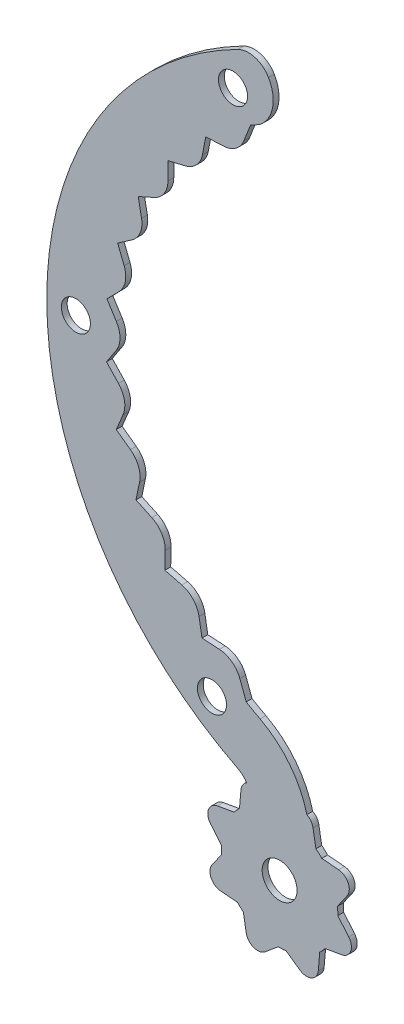
SolidWorks part; units mm, degrees
material "3003 Alaşım"
ref_plane "Ön Düzlem" through (0, 0, 0) normal (0, 0, 1) x (1, 0, 0)
ref_plane "Üst Düzlem" through (0, 0, 0) normal (0, 1, 0) x (1, 0, 0)
ref_plane "Sağ Düzlem" through (0, 0, 0) normal (1, 0, 0) x (0, 0, -1)
sketch "Çizim1" plane through (0, 0, 0) normal (0, 0, 1) x (1, 0, 0)
  line L0 (-50, 0) -> (-25, 0) construction
  line L1 (-25, 74.7114) -> (-25, -57.8833) construction
  line L3 (-25, 43.3013) -> (-26.1465, 40.3921)
  line L10 (-32.6937, 37.73) -> (-33.2521, 34.7773)
  line L11 (-32.6937, 37.73) -> (-29.6915, 37.8626)
  line L12 (-39.1845, 30.9355) -> (-36.2603, 31.6283)
  line L13 (-39.1845, 30.9355) -> (-39.1797, 27.9304)
  line L14 (-44.2872, 23.0451) -> (-41.5446, 24.2736)
  line L15 (-44.2872, 23.0451) -> (-43.7194, 20.0942)
  line L16 (-47.8209, 14.3384) -> (-45.3571, 16.059)
  line L17 (-47.8209, 14.3384) -> (-46.7103, 11.546)
  line L18 (-49.6606, 5.1236) -> (-47.5629, 7.2754)
  line L19 (-49.6606, 5.1236) -> (-48.0464, 2.5889)
  line L20 (-49.7411, -4.2726) -> (-48.0837, -1.7658)
  line L21 (-49.7411, -4.2726) -> (-47.6805, -6.46)
  line L22 (-48.0594, -13.5175) -> (-46.9011, -10.7445)
  line L23 (-48.0594, -13.5175) -> (-45.6255, -15.28)
  line L24 (-44.6753, -22.2835) -> (-44.057, -19.3426)
  line L25 (-44.6753, -22.2835) -> (-41.9541, -23.5587)
  line L26 (-39.7084, -30.2601) -> (-39.6522, -27.2555)
  line L27 (-39.7084, -30.2601) -> (-36.7965, -31.0028)
  line L28 (-33.3349, -37.1647) -> (-33.8427, -34.2028)
  line L29 (-33.3349, -37.1647) -> (-30.3354, -37.3487)
  line L30 (-25.7378, -42.8669) -> (-26.8343, -39.9385)
  line L31 (-25, -57.0526) -> (-25, -57.8833)
  line L33 (-15, -47.697) -> (-15, -66.5436) construction
  line L34 (-25, -66.5436) -> (-15, -66.5436) construction
  line L35 (-25, -54.5436) -> (-25, -66.5436) construction
  arc A0 (-27.1796, 53.4909) -> (-27.1875, -53.4868) centre (0, 0) ccw
  arc A3 (-23.4461, 44.162) -> (-21.9062, 51.9296) centre (-27.0983, 48.9224) ccw
  arc A4 (-26.1465, 40.3921) -> (-29.6915, 37.8626) centre (-29.8679, 41.8587) cw
  arc A5 (-33.2521, 34.7773) -> (-36.2603, 31.6283) centre (-37.1824, 35.5206) cw
  arc A6 (-39.1797, 27.9304) -> (-41.5446, 24.2736) centre (-43.1797, 27.9241) cw
  arc A7 (-43.7194, 20.0942) -> (-45.3571, 16.059) centre (-47.6474, 19.3384) cw
  arc A8 (-46.7103, 11.546) -> (-47.5629, 7.2754) centre (-50.4271, 10.0677) cw
  arc A9 (-48.0464, 2.5889) -> (-48.0837, -1.7658) centre (-51.4203, 0.4403) cw
  arc A10 (-47.6805, -6.46) -> (-46.9011, -10.7445) centre (-50.592, -9.2028) cw
  arc A11 (-45.6255, -15.28) -> (-44.057, -19.3426) centre (-47.9715, -18.5198) cw
  arc A12 (-41.9541, -23.5587) -> (-39.6522, -27.2555) centre (-43.6515, -27.1807) cw
  arc A13 (-36.7965, -31.0028) -> (-33.8427, -34.2028) centre (-37.7852, -34.8787) cw
  arc A14 (-30.3354, -37.3487) -> (-26.8343, -39.9385) centre (-30.5803, -41.3412) cw
  arc A15 (-23.4461, 44.162) -> (-25, 43.3013) centre (0, 0) ccw
  arc A16 (-20.8333, 45.453) -> (-15, -47.697) centre (0, 0) ccw construction
  arc A17 (-23.3522, -44.2117) -> (-14.8293, -57.9841) centre (-30.8249, -58.3594) cw
  arc A18 (-25, -57.8833) -> (-14.8293, -57.9841) centre (-20, -66.5436) ccw
  arc A19 (-25, 54.5436) -> (-25, -54.5436) centre (0, 0) ccw construction
  arc A20 (-27.1875, -53.4868) -> (-25, -57.0526) centre (-29, -57.0526) cw
  arc A21 (-27.1796, 53.4909) -> (-21.9062, 51.9296) centre (-25.3676, 49.9248) cw
  circle A22 centre (-20, -66.5436) radius 5
  arc A23 (-25.7378, -42.8669) -> (-23.3522, -44.2117) centre (0, 0) ccw
  circle A26 centre (-31.6201, -45.0019) radius 2.5
  circle A27 centre (-55, 0) radius 2.5
  circle A28 centre (-28.0006, 47.3388) radius 2.5
  point P9 (-25, 0)
  point P64 (-25, -54.5436)
  point P69 (0, 0)
  dimension "D1" = 60
  dimension "D2" = 10
  dimension "D4" = 4
  dimension "D6" = 16
  dimension "D7" = 4
  dimension "D8" = 4
  dimension "D9" = 10
  dimension "D3" = 25
  dimension "D5" = 11
extrude "Yükseklik-Ekstrüzyon2" add sketch "Çizim1" along normal blind 1
sketch "Çizim2" plane through (0, 0, 1) normal (0, 0, 1) x (1, 0, 0)
  line L0 (-14.2682, -55.8596) -> (-13.7465, -58.818)
  line L17 (-25.7318, -77.2275) -> (-26.2535, -74.2691)
  line L18 (-16.5798, -57.1466) -> (-14.8697, -52.4482) construction
  line L19 (-26.6412, -56.3999) -> (-26.903, -59.3924)
  line L20 (-30.6839, -60.8117) -> (-27.7256, -60.2901)
  line L21 (-8.1313, -69.0202) -> (-10.0622, -66.719)
  line L22 (-9.3161, -72.2754) -> (-12.2744, -72.797)
  line L23 (-8.3923, -63.0419) -> (-10.1153, -65.5026)
  line L24 (-13.3588, -76.6873) -> (-13.097, -73.6947)
  line L25 (-22.4766, -78.4123) -> (-20.1754, -76.4813)
  line L26 (-17.5234, -54.6749) -> (-19.8246, -56.6058)
  line L27 (-31.8687, -64.0669) -> (-29.9378, -66.3681)
  line L28 (-23.5016, -54.9359) -> (-21.0409, -56.6589)
  line L29 (-30.1437, -73.1848) -> (-27.1511, -73.4466)
  line L30 (-16.4984, -78.1513) -> (-18.9591, -76.4282)
  line L31 (-31.6077, -70.0452) -> (-29.8847, -67.5845)
  line L32 (-9.8563, -59.9024) -> (-12.8489, -59.6406)
  arc A38 (-25.7318, -77.2275) -> (-22.4766, -78.4123) centre (-23.7622, -76.8802) ccw
  arc A39 (-13.097, -73.6947) -> (-12.2744, -72.797) centre (-12.1008, -73.7818) cw
  arc A40 (-8.3923, -63.0419) -> (-9.8563, -59.9024) centre (-10.0306, -61.8948) ccw
  arc A41 (-27.7256, -60.2901) -> (-26.903, -59.3924) centre (-27.8992, -59.3053) ccw
  arc A42 (-23.5016, -54.9359) -> (-26.6412, -56.3999) centre (-24.6488, -56.5742) ccw
  arc A43 (-14.2682, -55.8596) -> (-17.5234, -54.6749) centre (-16.2378, -56.2069) ccw
  arc A44 (-31.6077, -70.0452) -> (-30.1437, -73.1848) centre (-29.9694, -71.1924) ccw
  arc A45 (-10.0622, -66.719) -> (-10.1153, -65.5026) centre (-9.2962, -66.0762) cw
  circle A46 centre (-20, -66.5436) radius 10 construction
  arc A47 (-16.4984, -78.1513) -> (-13.3588, -76.6873) centre (-15.3512, -76.5129) ccw
  arc A48 (-29.8847, -67.5845) -> (-29.9378, -66.3681) centre (-30.7038, -67.0109) ccw
  arc A49 (-12.8489, -59.6406) -> (-13.7465, -58.818) centre (-12.7617, -58.6444) cw
  arc A50 (-19.8246, -56.6058) -> (-21.0409, -56.6589) centre (-20.4673, -55.8397) cw
  arc A51 (-20.1754, -76.4813) -> (-18.9591, -76.4282) centre (-19.5327, -77.2474) cw
  arc A52 (-30.6839, -60.8117) -> (-31.8687, -64.0669) centre (-30.3366, -62.7813) ccw
  arc A53 (-27.1511, -73.4466) -> (-26.2535, -74.2691) centre (-27.2383, -74.4428) cw
  arc A54 (-9.3161, -72.2754) -> (-8.1313, -69.0202) centre (-9.6634, -70.3058) ccw
  circle A55 centre (-20, -66.5436) radius 3
  point P48 (-20, -66.5436)
extrude "Yükseklik-Ekstrüzyon4" add sketch "Çizim2" against normal blind 1
